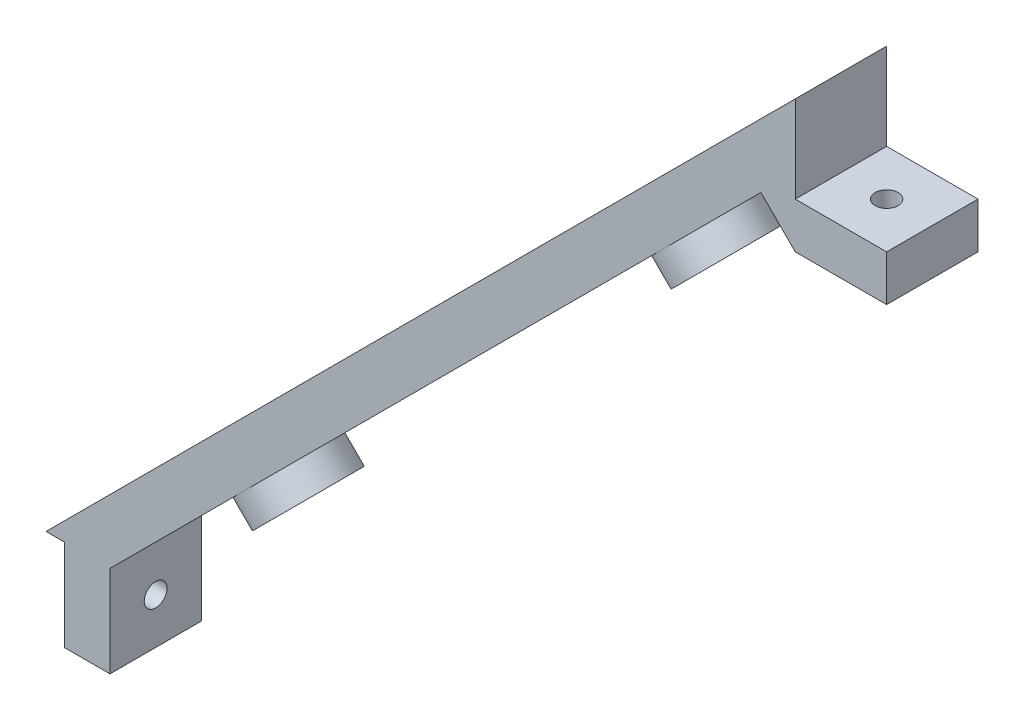
SolidWorks part; units mm, degrees
ref_plane "Front Plane" through (0, 0, 0) normal (0, 0, 1) x (1, 0, 0)
ref_plane "Top Plane" through (0, 0, 0) normal (0, 1, 0) x (1, 0, 0)
ref_plane "Right Plane" through (0, 0, 0) normal (1, 0, 0) x (0, 0, -1)
sketch "Sketch1" plane through (0, 0, 0) normal (0, 0, 1) x (1, 0, 0)
  line L0 (-41, -41) -> (41, 41)
  line L1 (41, 41) -> (41, 31.5)
  line L2 (-39, -41) -> (-39, -51)
  line L3 (-39, -51) -> (-34, -51)
  line L4 (41, 26.5) -> (37.25, 30.25)
  line L5 (-34, -51) -> (-34, -41)
  line L6 (-41, -41) -> (-39, -41)
  line L7 (-34, -41) -> (37.25, 30.25)
  line L8 (51, 31.5) -> (41, 31.5)
  line L9 (51, 31.5) -> (51, 26.5)
  line L10 (41, 26.5) -> (51, 26.5)
  point P13 (0, 0)
  dimension "D1" = 45
  dimension "D2" = 10
  dimension "D3" = 5
  dimension "D4" = 80
  dimension "D5" = 115.9655
  dimension "D7" = 9.5
  dimension "D8" = 2
extrude "Main" add sketch "Sketch1" along normal mid plane 10
sketch "Sketch2" plane through (41, 0, 0) normal (1, 0, 0) x (0, 0, -1)
  line L0 (5, -41) -> (-5, -51) construction
  line L1 (-5, -41) -> (5, -51) construction
  circle A0 centre (0, -46) radius 1.25
  dimension "D1" = 2.5
extrude "FixHole1" cut sketch "Sketch2" against normal through all
sketch "Sketch3" plane through (0, 31.5, 0) normal (0, -1, 0) x (-1, 0, 0)
  line L0 (-51, -5) -> (-41, -5) construction
  line L1 (-41, -5) -> (-41, 5) construction
  line L4 (-41, 5) -> (-51, -5) construction
  line L5 (-41, -5) -> (-51, 5) construction
  circle A1 centre (-46, 0) radius 1.25
  point P0 (-41, 5)
  dimension "D1" = 2.5
extrude "FixHole2" cut sketch "Sketch3" along normal through all
sketch "Sketch7" plane through (3.5, -3.5, 0) normal (-0.7071, 0.7071, 0) x (0, 0, 1)
  line L0 (-5, 57.9828) -> (-5, -57.9828) construction
  circle A0 centre (0, -32.4) radius 5
  circle A1 centre (0, 32.4) radius 5
  dimension "D1" = 10
  dimension "D2" = 64.8
  dimension "D3" = 32.4
  dimension "D4" = 5
extrude "BoardSupport" add sketch "Sketch7" against normal blind 3
sketch "Sketch8" plane through (5.6213, -5.6213, 0) normal (0.7071, -0.7071, 0) x (0, 0, -1)
  circle A0 centre (0, 32.4) radius 1.25
  circle A1 centre (0, 32.4) radius 5 construction
  circle A2 centre (0, -32.4) radius 1.25
  circle A4 centre (0, -32.4) radius 5 construction
  dimension "D1" = 2.5
extrude "HoleFix" cut sketch "Sketch8" against normal through all
sketch "Sketch6" plane through (3.5, -3.5, 0) normal (-0.7071, 0.7071, 0) x (0, 0, 1)
  circle A0 centre (0, 40) radius 1.25
  dimension "D1" = 2.5
  dimension "D2" = 40
extrude "Cut-Extrude2" cut sketch "Sketch6" along normal through all
pattern_linear "LPattern1" count 5 spacing 20 along (-0.7071, -0.7071, 0) of "Cut-Extrude2"
